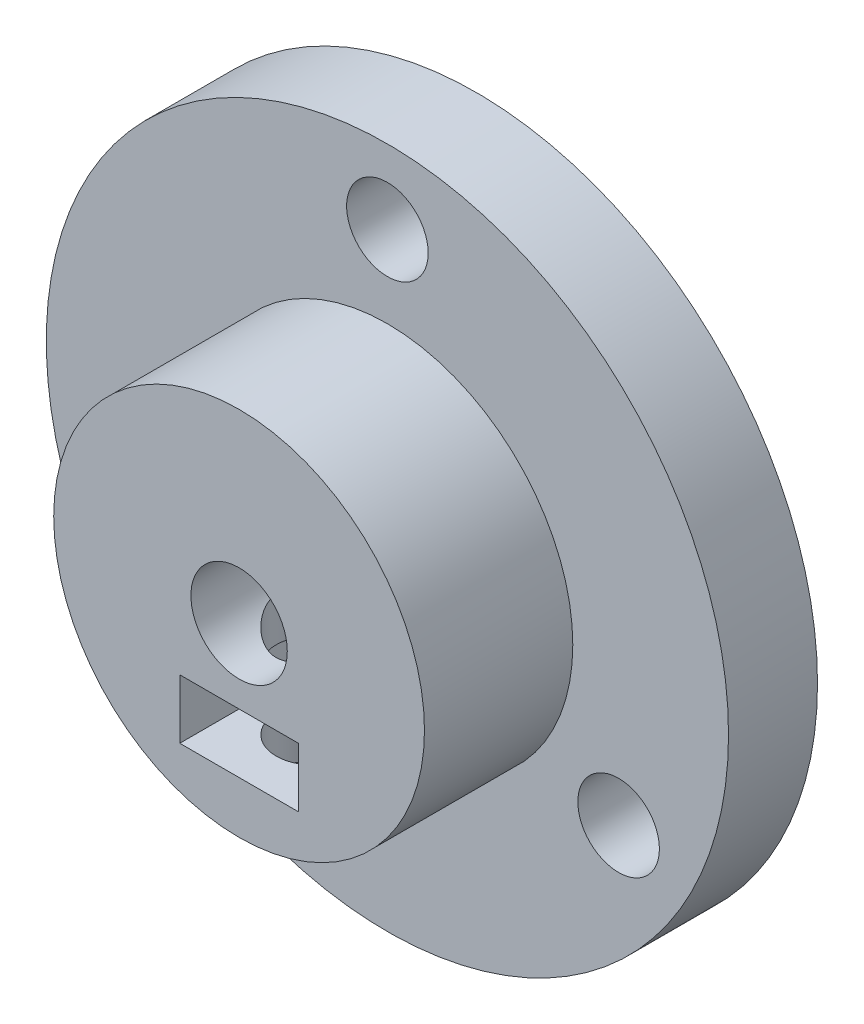
SolidWorks part; units mm, degrees
ref_plane "Plan de face" through (0, 0, 0) normal (0, 0, 1) x (1, 0, 0)
ref_plane "Plan de dessus" through (0, 0, 0) normal (0, 1, 0) x (1, 0, 0)
ref_plane "Plan de droite" through (0, 0, 0) normal (1, 0, 0) x (0, 0, -1)
sketch "Esquisse1" plane through (0, 0, 0) normal (0, 0, 1) x (1, 0, 0)
  circle A0 centre (0, 0) radius 23
  dimension "D1" = 46
extrude "Boss.-Extru.1" add sketch "Esquisse1" along normal blind 6
sketch "Esquisse2" plane through (0, 0, 6) normal (0, 0, 1) x (1, 0, 0)
  circle A0 centre (0, 0) radius 12.5
  dimension "D1" = 25
extrude "Boss.-Extru.2" add sketch "Esquisse2" along normal blind 10
sketch "Esquisse3" plane through (0, 0, 16) normal (0, 0, 1) x (1, 0, 0)
  circle A0 centre (0, 0) radius 3.25
  dimension "D1" = 6.5
extrude "Enlèv. mat.-Extru.1" cut sketch "Esquisse3" against normal up to surface (16 mm away) up to face at (23, 0, 0)
sketch "Esquisse4" plane through (0, 0, 0) normal (0, 1, 0) x (1, 0, 0)
  line L0 (-12.5, -6) -> (12.5, -6) construction
  circle A0 centre (0, -11) radius 2.5
  dimension "D1" = 5
  dimension "D2" = 5
extrude "Enlèv. mat.-Extru.2" cut sketch "Esquisse4" against normal up to surface (12.5 mm away)
sketch "Esquisse5" plane through (0, 0, 6) normal (0, 0, 1) x (1, 0, 0)
  circle A0 centre (0, 18) radius 2.75
  dimension "D2" = 5.5
  dimension "D1" = 18
extrude "Enlèv. mat.-Extru.3" cut sketch "Esquisse5" against normal up to surface (6 mm away) contours A0 up to face at (3.25, 0, 0)
pattern_curve "Répét. par courbe1" of "Enlèv. mat.-Extru.3" parameters "D1"=3, "D3"=10, "D2"=1, "D4"=10
sketch "Esquisse6" plane through (0, 0, 16) normal (0, 0, 1) x (1, 0, 0)
  line L1 (-4, -5) -> (4, -5)
  line L2 (-4, -5) -> (-4, -9)
  line L3 (-4, -9) -> (4, -9)
  line L4 (4, -5) -> (4, -9)
  line L5 (-4, -5) -> (4, -9) construction
  line L6 (-4, -9) -> (4, -5) construction
  arc A0 (-2.5, -12.2474) -> (2.5, -12.2474) centre (0, 0) ccw construction
  circle A1 centre (0, 0) radius 12.5 construction
  point P0 (0, -7)
  dimension "D1" = 8
  dimension "D2" = 0
  dimension "D3" = 4
  dimension "D4" = 7
extrude "Enlèv. mat.-Extru.4" cut sketch "Esquisse6" against normal up to surface (10 mm away) up to face at (14.2135, -11.3816, 6)
